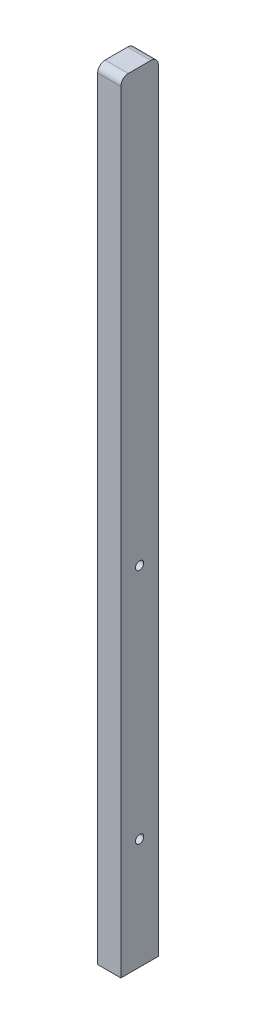
SolidWorks part; units mm, degrees
material "Cedar"
ref_plane "Front Plane" through (0, 0, 0) normal (0, 0, 1) x (1, 0, 0)
ref_plane "Top Plane" through (0, 0, 0) normal (0, 1, 0) x (1, 0, 0)
ref_plane "Right Plane" through (0, 0, 0) normal (1, 0, 0) x (0, 0, -1)
sketch "Sketch1" plane through (0, 0, 0) normal (0, 1, 0) x (1, 0, 0)
  line L1 (7.75, -12.5) -> (-7.75, -12.5)
  line L2 (7.75, -12.5) -> (7.75, 12.5)
  line L3 (7.75, 12.5) -> (-7.75, 12.5)
  line L4 (-7.75, -12.5) -> (-7.75, 12.5)
  line L5 (7.75, -12.5) -> (-7.75, 12.5) construction
  line L6 (7.75, 12.5) -> (-7.75, -12.5) construction
  point P0 (0, 0)
  dimension "D1" = 15.5
  dimension "D2" = 25
extrude "Boss-Extrude1" add sketch "Sketch1" along normal blind 520
fillet "Fillet1" radius 5 2 edges at (0, 520, 12.5) (0, 520, -12.5)
sketch "Sketch4" plane through (0, 0, 0) normal (0, -1, 0) x (-1, 0, 0)
  point P0 (0, 0)
hole_wizard "Ø5.0mm Dowel Hole1" positions "Sketch4" profile "Sketch3" hole size "Ø5.0" standard "ISO"
sketch "Sketch3" plane through (0, 0, 0) normal (1, 0, 0) x (0, 0, -1)
  line L0 (0, 0) -> (0, 13.9828)
  line L1 (0, 13.9828) -> (3.3, 12)
  line L2 (3.3, 12) -> (3.3, 0)
  line L5 (3.3, 0) -> (0, 0)
  line L10 (0, 13.9828) -> (-3.3, 12) construction
  line L11 (0, -6.35) -> (0, 107.95) construction
  dimension "Hole Dia." = 6.6
  dimension "Hole Depth" = 12
  dimension "Drill Angle" = 118
sketch "Sketch11" plane through (-7.75, 0, 0) normal (-1, 0, 0) x (0, 0, 1)
  line L0 (-12.5, 0) -> (12.5, 0) construction
  point P0 (0, 74)
  point P5 (0, 232)
  dimension "D1" = 74
  dimension "D2" = 232
hole_wizard "CBORE for M5 Hex Socket Head Cap Screw2" positions "Sketch11" profile "Sketch10" counterbore size "M5" standard "ISO" end condition through all
sketch "Sketch10" plane through (-7.75, 74, 0) normal (0, 1, 0) x (0, 0, 1)
  line L0 (0, 0) -> (0, 15.5)
  line L1 (0, 15.5) -> (2.75, 15.5)
  line L3 (2.75, 15.5) -> (2.75, 5.4)
  line L4 (2.75, 5.4) -> (5, 5.4)
  line L5 (5, 5.4) -> (5, 0)
  line L7 (5, 0) -> (0, 0)
  line L11 (0, -6.35) -> (0, 107.95) construction
  dimension "Thru Hole Dia." = 5.5
  dimension "Thru Hole Depth" = 15.5
  dimension "C'Bore Dia." = 10
  dimension "C'Bore Depth" = 5.4
